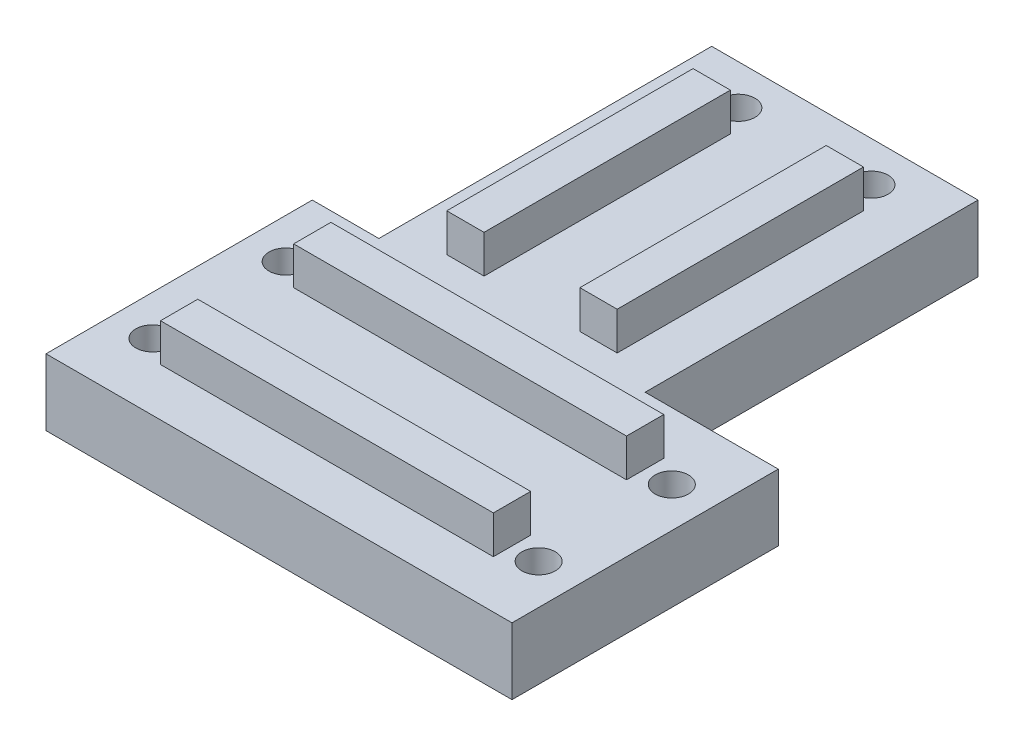
SolidWorks part; units mm, degrees
ref_plane "Alzado" through (0, 0, 0) normal (0, 0, 1) x (1, 0, 0)
ref_plane "Planta" through (0, 0, 0) normal (0, 1, 0) x (1, 0, 0)
ref_plane "Vista lateral" through (0, 0, 0) normal (1, 0, 0) x (0, 0, -1)
sketch "Croquis1" plane through (0, 0, 0) normal (0, 1, 0) x (1, 0, 0)
  line L1 (20, 20) -> (-30, 20)
  line L3 (40, -20) -> (-30, -20)
  line L4 (-30, 20) -> (-30, -20)
  line L7 (40, -20) -> (70, -20)
  line L9 (20, 20) -> (70, 20)
  line L10 (70, -20) -> (70, 20)
  point P0 (0, 0)
  dimension "D1" = 40
  dimension "D2" = 50
  dimension "D3" = 50
  dimension "D4" = 30
  dimension "D5" = 20
extrude "Saliente-Extruir1" add sketch "Croquis1" along normal blind 10
sketch "Croquis3" plane through (-30, 0, 0) normal (-1, 0, 0) x (0, 0, 1)
  line L0 (10, 15.7) -> (10, 4.4945) construction
  line L21 (10, 10) -> (12.8, 10)
  line L29 (20, 10) -> (-20, 10) construction
  line L30 (12.8, 10) -> (12.8, 15.7)
  line L33 (20, 10) -> (20, 0) construction
  line L34 (12.8, 15.7) -> (7.2, 15.7)
  line L35 (7.2, 15.7) -> (7.2, 10)
  line L47 (7.2, 10) -> (10, 10)
  line L59 (-10, 10) -> (-7.2, 10)
  line L60 (-7.2, 10) -> (-7.2, 15.7)
  line L61 (-7.2, 15.7) -> (-12.8, 15.7)
  line L62 (-12.8, 15.7) -> (-12.8, 10)
  line L63 (-12.8, 10) -> (-10, 10)
  line L64 (-10, 15.7) -> (-10, 4.4945) construction
  dimension "D1" = 2.8
  dimension "D2" = 10
  dimension "D3" = 2.8
  dimension "D4" = 5.7
  dimension "D5" = 2
extrude "Saliente-Extruir3" add sketch "Croquis3" against normal blind 100
sketch "Croquis5" plane through (0, 10, 0) normal (0, 1, 0) x (1, 0, 0)
  line L0 (-30, -12.8) -> (-30, -20) construction
  line L1 (-20, 70) -> (20, 70)
  line L2 (-20, 70) -> (-20, 20)
  line L3 (-20, 20) -> (20, 20)
  line L4 (20, 70) -> (20, 20)
  line L6 (70, 20) -> (-30, 20) construction
  dimension "D1" = 10
  dimension "D2" = 40
  dimension "D3" = 50
extrude "Saliente-Extruir5" add sketch "Croquis5" against normal blind 10
sketch "Croquis7" plane through (0, 0, -70) normal (0, 0, -1) x (-1, 0, 0)
  line L0 (-10, 12.7) -> (-10, 2.6944) construction
  line L14 (-20, 0) -> (-20, 10) construction
  line L16 (-10, 10) -> (-12.8, 10)
  line L17 (-70, 10) -> (30, 10) construction
  line L43 (-20, 10) -> (20, 10) construction
  line L44 (-12.8, 10) -> (-12.8, 15.7)
  line L45 (-70, 15.7) -> (30, 15.7) construction
  line L46 (-12.8, 15.7) -> (-7.2, 15.7)
  line L47 (-7.2, 15.7) -> (-7.2, 10)
  line L48 (-7.2, 10) -> (-10, 10)
  line L49 (10, 10) -> (7.2, 10)
  line L50 (7.2, 10) -> (7.2, 15.7)
  line L51 (7.2, 15.7) -> (12.8, 15.7)
  line L52 (12.8, 15.7) -> (12.8, 10)
  line L53 (12.8, 10) -> (10, 10)
  line L54 (10, 12.7) -> (10, 2.6944) construction
  dimension "D1" = 10
  dimension "D2" = 2.8
  dimension "D3" = 2.8
  dimension "D4" = 2
extrude "Saliente-Extruir7" add sketch "Croquis7" against normal blind 47
sketch "Croquis13" plane through (70, 0, 0) normal (1, 0, 0) x (0, 0, -1)
  line L1 (-29.6381, 22.1993) -> (29.6381, 22.1993)
  line L2 (-29.6381, 22.1993) -> (-29.6381, -22.1993)
  line L3 (-29.6381, -22.1993) -> (29.6381, -22.1993)
  line L4 (29.6381, 22.1993) -> (29.6381, -22.1993)
  line L5 (-29.6381, 22.1993) -> (29.6381, -22.1993) construction
  line L6 (-29.6381, -22.1993) -> (29.6381, 22.1993) construction
extrude "Cortar-Extruir4" cut sketch "Croquis13" against normal blind 30
sketch "Croquis14" plane through (0, 0, 0) normal (0, -1, 0) x (-1, 0, 0)
  line L0 (30, -20) -> (-40, -20) construction
  line L1 (-40, 20) -> (-40, -20) construction
  line L2 (30, 20) -> (30, -20) construction
  line L3 (20, 70) -> (20, 20) construction
  line L4 (-20, 70) -> (20, 70) construction
  circle A0 centre (-34, -10) radius 2.5
  circle A1 centre (-34, 10) radius 2.5
  circle A2 centre (24, -10) radius 2.5
  circle A3 centre (24, 10) radius 2.5
  circle A4 centre (10, 64) radius 2.5
  circle A5 centre (-10, 64) radius 2.5
  dimension "D1" = 5
  dimension "D2" = 10
  dimension "D3" = 20
  dimension "D4" = 6
  dimension "D5" = 6
  dimension "D6" = 10
  dimension "D7" = 20
  dimension "D8" = 6
extrude "Cortar-Extruir5" cut sketch "Croquis14" against normal through all
sketch "Croquis15" plane through (0, 10, 0) normal (0, 1, 0) x (1, 0, 0)
  line L0 (40, 20) -> (20, 20) construction
  line L1 (40, -20) -> (30, -20)
  line L2 (40, -20) -> (40, 20)
  line L3 (40, 20) -> (30, 20)
  line L4 (30, -20) -> (30, 20)
  line L5 (20, 20) -> (20, 70) construction
  line L6 (-30, -20) -> (-20, -20)
  line L7 (-30, -20) -> (-30, 20)
  line L8 (-30, 20) -> (-20, 20)
  line L9 (-20, -20) -> (-20, 20)
  line L10 (-20, 70) -> (20, 70)
  line L11 (-20, 70) -> (-20, 60)
  line L12 (-20, 60) -> (20, 60)
  line L13 (20, 70) -> (20, 60)
  dimension "D1" = 10
  dimension "D2" = 10
extrude "Cortar-Extruir6" cut sketch "Croquis15" along normal through all
